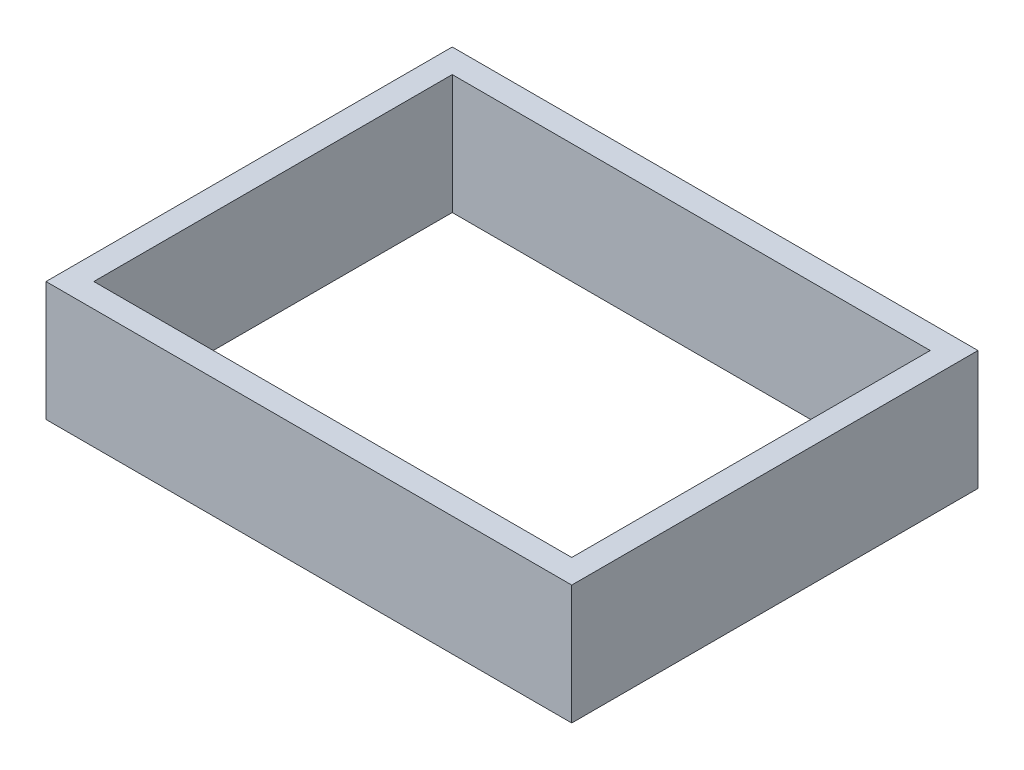
SolidWorks part; units mm, degrees
ref_plane "前视基准面" through (0, 0, 0) normal (0, 0, 1) x (1, 0, 0)
ref_plane "上视基准面" through (0, 0, 0) normal (0, 1, 0) x (1, 0, 0)
ref_plane "右视基准面" through (0, 0, 0) normal (1, 0, 0) x (0, 0, -1)
sketch "草图1" plane through (0, 0, 0) normal (0, 1, 0) x (1, 0, 0)
  line L0 (-22, -17) -> (-22, 17)
  line L1 (-20, -15) -> (20, -15)
  line L2 (-20, -15) -> (-20, 15)
  line L3 (-20, 15) -> (20, 15)
  line L4 (20, -15) -> (20, 15)
  line L5 (-20, -15) -> (20, 15) construction
  line L6 (-20, 15) -> (20, -15) construction
  line L7 (-22, 17) -> (22, 17)
  line L8 (22, -17) -> (22, 17)
  line L9 (-22, -17) -> (22, -17)
  point P0 (0, 0)
  dimension "D1" = 2
extrude "凸台-拉伸1" add sketch "草图1" along normal blind 10
